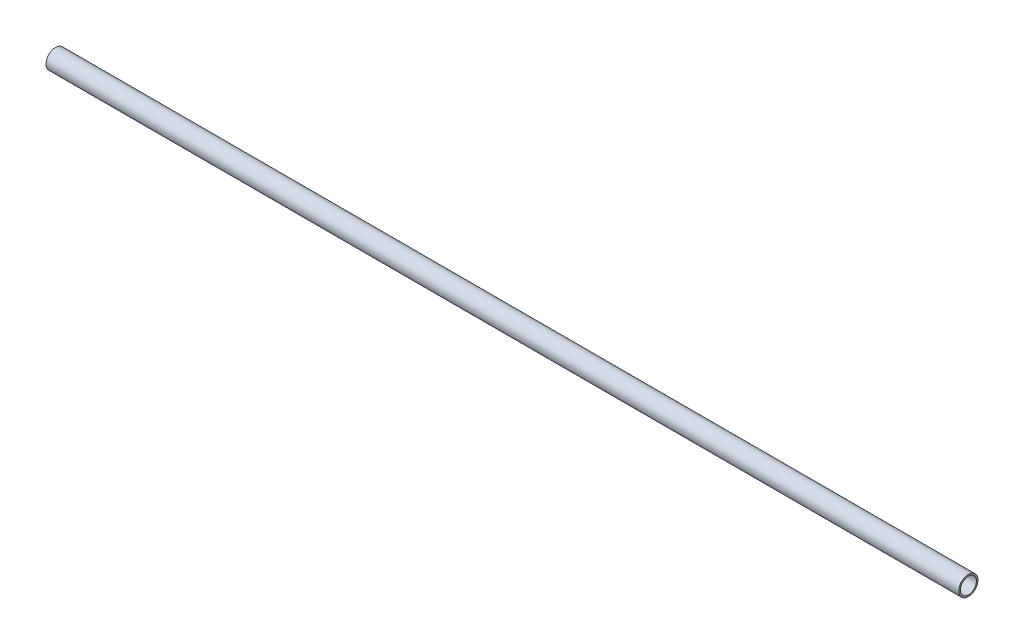
SolidWorks part; units mm, degrees
ref_plane "Front Plane" through (0, 0, 0) normal (0, 0, 1) x (1, 0, 0)
ref_plane "Top Plane" through (0, 0, 0) normal (0, 1, 0) x (1, 0, 0)
ref_plane "Right Plane" through (0, 0, 0) normal (1, 0, 0) x (0, 0, -1)
sketch "Sketch1" plane through (0, 0, 0) normal (1, 0, 0) x (0, 0, -1)
  circle A0 centre (0, 0) radius 3.175
  circle A1 centre (0, 0) radius 2.667
  dimension "D1" = 6.35
  dimension "D2" = 0.508
extrude "Boss-Extrude1" add sketch "Sketch1" against normal blind 301.625
